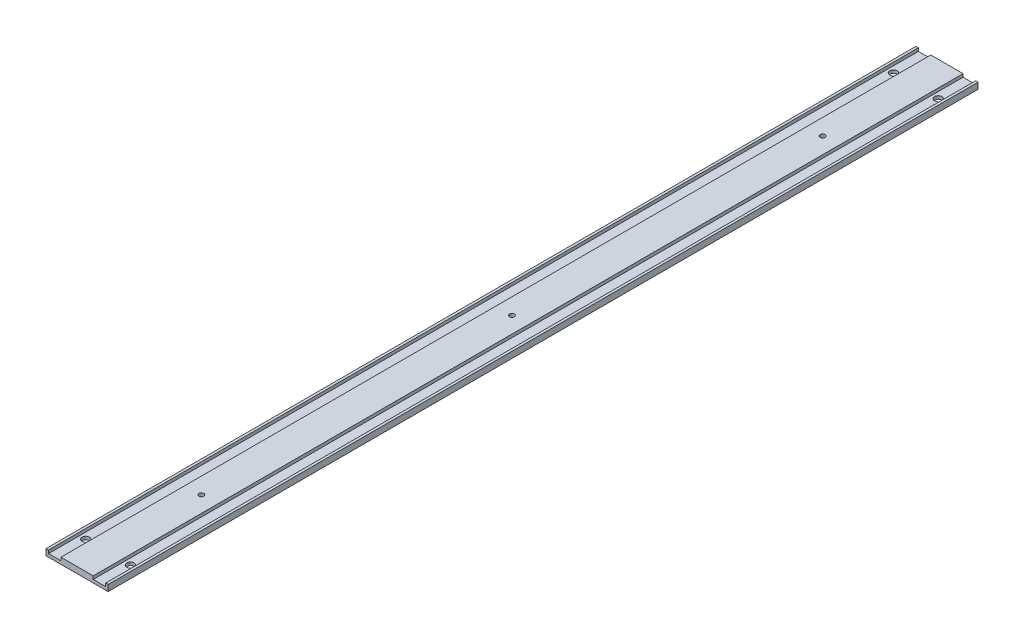
SolidWorks part; units mm, degrees
ref_plane "Front Plane" through (0, 0, 0) normal (0, 0, 1) x (1, 0, 0)
ref_plane "Top Plane" through (0, 0, 0) normal (0, 1, 0) x (1, 0, 0)
ref_plane "Right Plane" through (0, 0, 0) normal (1, 0, 0) x (0, 0, -1)
sketch "Sketch1" plane through (0, 0, 0) normal (0, 1, 0) x (1, 0, 0)
  line L0 (0, 0) -> (50, 0)
  line L1 (50, 0) -> (50, 700)
  line L2 (50, 700) -> (0, 700)
  line L3 (0, 700) -> (0, 0)
  dimension "D1" = 700
  dimension "D2" = 50
extrude "Boss-Extrude1" add sketch "Sketch1" along normal blind 5
sketch "Sketch3" plane through (0, 5, 0) normal (0, 1, 0) x (1, 0, 0)
  circle A0 centre (25, 600) radius 2
  circle A1 centre (25, 350) radius 2
  circle A2 centre (25, 100) radius 2
  dimension "D4" = 4
  dimension "D5" = 4
  dimension "D6" = 4
extrude "Cut-Extrude1" cut sketch "Sketch3" against normal through all
sketch "Sketch5" plane through (0, 5, 0) normal (0, 1, 0) x (1, 0, 0)
  line L0 (2, 700) -> (12, 700)
  line L1 (38, 700) -> (48, 700)
  line L2 (48, 0) -> (48, 700)
  line L4 (38, 0) -> (48, 0)
  line L5 (38, 700) -> (38, 0)
  line L7 (12, 0) -> (2, 0)
  line L8 (12, 0) -> (12, 700)
  line L9 (2, 700) -> (2, 0)
extrude "Cut-Extrude2" cut sketch "Sketch5" against normal blind 2.5
sketch "Sketch6" plane through (0, 5, 0) normal (0, 1, 0) x (1, 0, 0)
  circle A0 centre (43, 25) radius 3
  circle A1 centre (7, 25) radius 3
  circle A2 centre (43, 675) radius 3
  circle A3 centre (7, 675) radius 3
extrude "Cut-Extrude3" cut sketch "Sketch6" against normal through all
